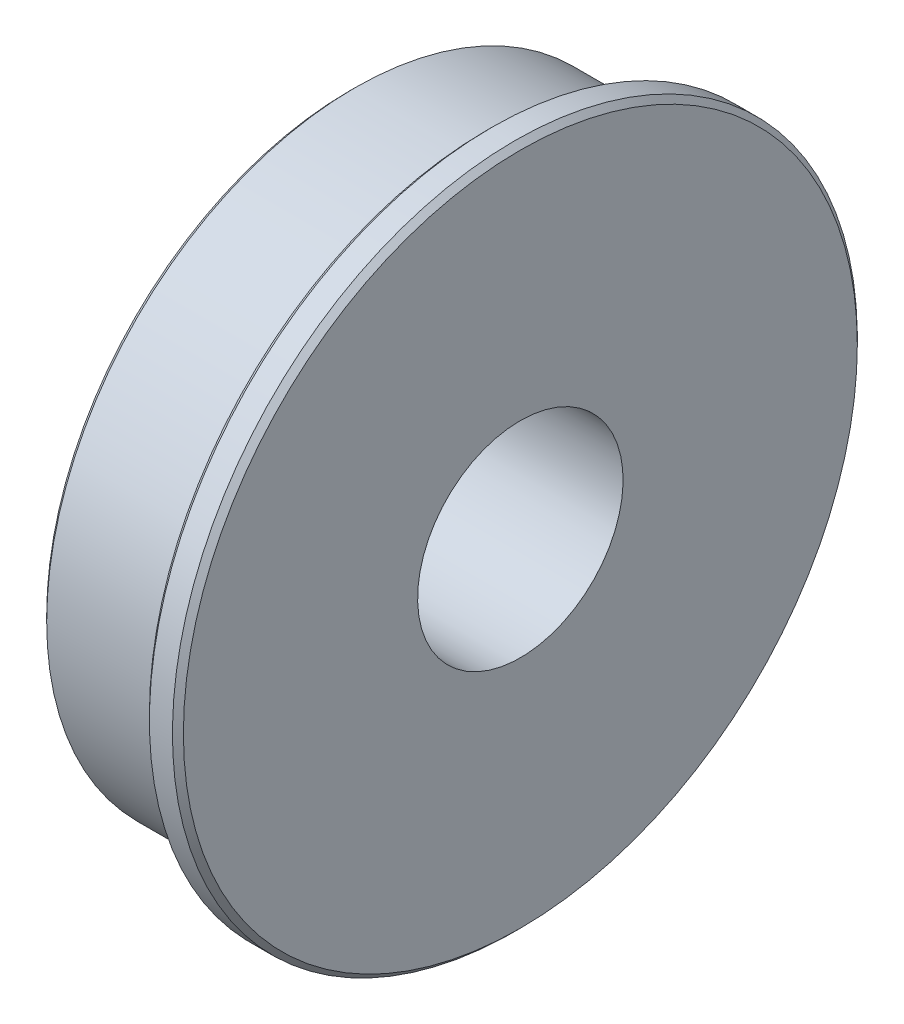
SolidWorks part; units mm, degrees
ref_plane "Front Plane" through (0, 0, 0) normal (0, 0, 1) x (1, 0, 0)
ref_plane "Top Plane" through (0, 0, 0) normal (0, 1, 0) x (1, 0, 0)
ref_plane "Right Plane" through (0, 0, 0) normal (1, 0, 0) x (0, 0, -1)
sketch "Sketch1" plane through (0, 0, 0) normal (0, 0, 1) x (1, 0, 0)
  line L0 (3.9624, 0) -> (-3.9624, 0) construction
  line L1 (-3.9624, 0) -> (-3.9624, 14.2875) construction
  line L2 (-3.9624, 14.2875) -> (2.3876, 14.2875)
  line L3 (2.3876, 14.2875) -> (2.3876, 15.875)
  line L4 (2.3876, 15.875) -> (3.9624, 15.875)
  line L5 (3.9624, 15.875) -> (3.9624, 0) construction
  line L6 (-3.9624, 14.2875) -> (-3.9624, 4.7625)
  line L7 (-3.9624, 4.7625) -> (3.9624, 4.7625)
  line L8 (3.9624, 4.7625) -> (3.9624, 15.875)
  point P4 (0, 0)
  dimension "D1" = 9.525
  dimension "D2" = 7.9248
  dimension "D3" = 1.5748
  dimension "D4" = 31.75
  dimension "D5" = 28.575
revolve "Revolve1" add sketch "Sketch1" angle 360 about L0
chamfer "Chamfer1" distance 0.254 angle 45 3 edges at (3.9624, 15.875, 0) (2.3876, 15.875, 0) (-3.9624, 14.2875, 0)
